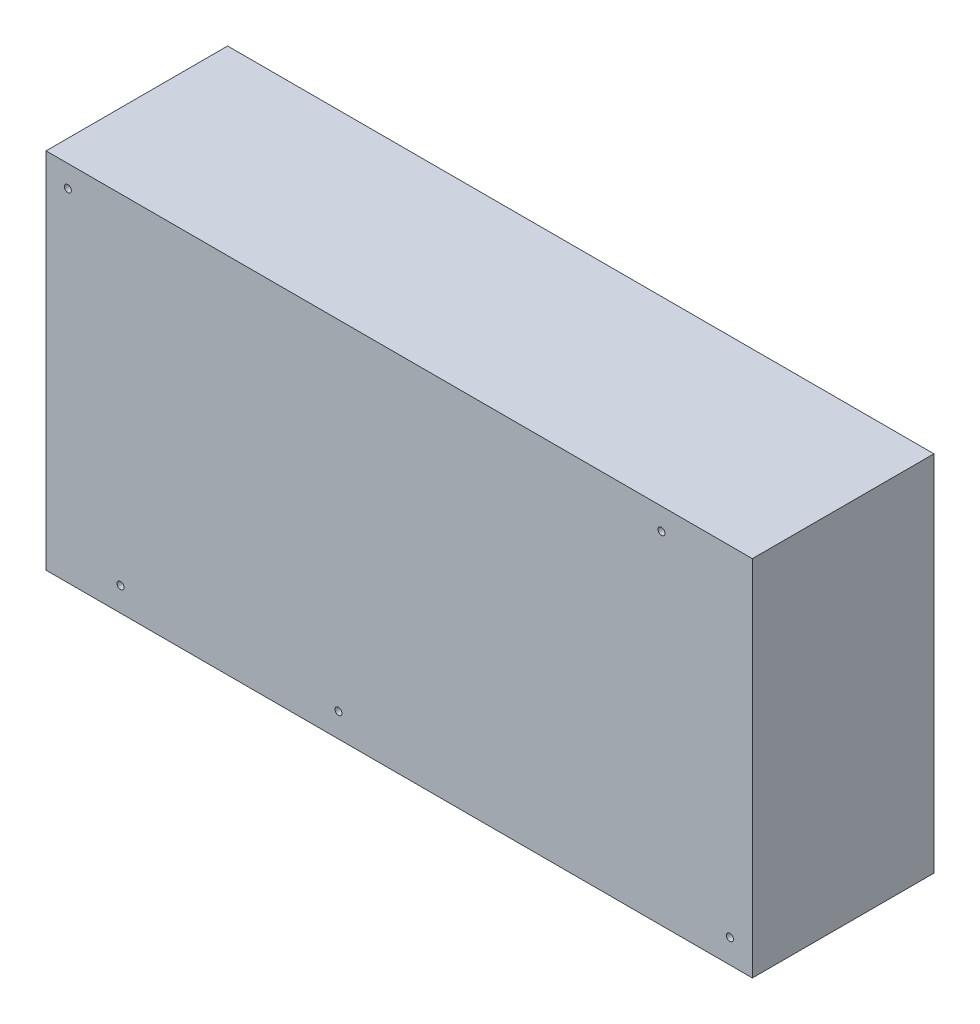
SolidWorks part; units mm, degrees
ref_plane "Front Plane" through (0, 0, 0) normal (0, 0, 1) x (1, 0, 0)
ref_plane "Top Plane" through (0, 0, 0) normal (0, 1, 0) x (1, 0, 0)
ref_plane "Right Plane" through (0, 0, 0) normal (1, 0, 0) x (0, 0, -1)
sketch "Sketch1" plane through (0, 0, 0) normal (0, 0, 1) x (1, 0, 0)
  line L1 (123.5, -63.5) -> (-123.5, -63.5)
  line L2 (123.5, -63.5) -> (123.5, 63.5)
  line L3 (123.5, 63.5) -> (-123.5, 63.5)
  line L4 (-123.5, -63.5) -> (-123.5, 63.5)
  line L5 (123.5, -63.5) -> (-123.5, 63.5) construction
  line L6 (123.5, 63.5) -> (-123.5, -63.5) construction
  point P0 (0, 0)
  dimension "D1" = 247
  dimension "D2" = 127
extrude "Boss-Extrude1" add sketch "Sketch1" along normal blind 63.5
hole_wizard "#41 (0.096) Diameter Hole1" positions "Sketch3" profile "Sketch2" hole size "#41" standard "ANSI Inch" end condition through all
sketch "Sketch3" plane through (0, 0, 63.5) normal (0, 0, 1) x (1, 0, 0)
  line L0 (-123.5, 63.5) -> (-123.5, -63.5) construction
  line L1 (123.5, 63.5) -> (-123.5, 63.5) construction
  line L2 (-123.5, -63.5) -> (123.5, -63.5) construction
  point P0 (-115.88, 55.88)
  point P2 (-97.465, -55.118)
  point P4 (-21.265, -55.118)
  point P6 (115.641, -55.118)
  point P8 (91.7015, 55.88)
  dimension "D1" = 207.5815
  dimension "D2" = 7.62
  dimension "D3" = 7.62
  dimension "D4" = 8.382
  dimension "D5" = 26.035
  dimension "D6" = 76.2
  dimension "D7" = 136.906
sketch "Sketch2" plane through (-115.88, 55.88, 63.5) normal (1, 0, 0) x (0, -1, 0)
  line L0 (0, 0) -> (0, 63.5)
  line L1 (0, 63.5) -> (1.2192, 63.5)
  line L2 (1.2192, 63.5) -> (1.2192, 0)
  line L5 (1.2192, 0) -> (0, 0)
  line L11 (0, -6.35) -> (0, 107.95) construction
  dimension "Thru Hole Dia." = 2.4384
  dimension "Thru Hole Depth" = 63.5
